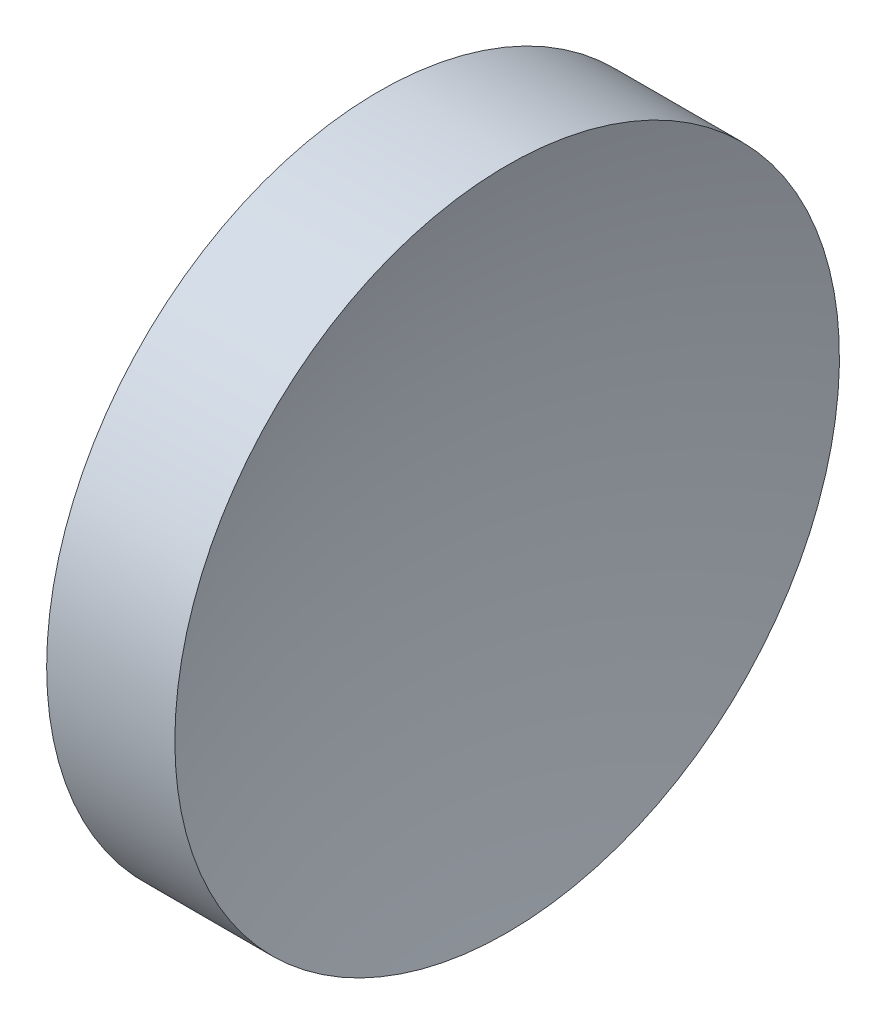
SolidWorks part; units mm, degrees
ref_plane "前视基准面" through (0, 0, 0) normal (0, 0, 1) x (1, 0, 0)
ref_plane "上视基准面" through (0, 0, 0) normal (0, 1, 0) x (1, 0, 0)
ref_plane "右视基准面" through (0, 0, 0) normal (1, 0, 0) x (0, 0, -1)
sketch "草图1" plane through (0, 0, 0) normal (0, 0, 1) x (1, 0, 0)
  line L0 (111.9552, 71.194) -> (137.836, 71.194) construction
  line L1 (119.5068, 71.194) -> (119.5068, 83.894)
  line L2 (119.5068, 83.894) -> (124.4066, 83.894)
  line L3 (122.5068, 71.194) -> (119.5068, 71.194)
  arc A0 (124.4066, 83.894) -> (122.5068, 71.194) centre (165.9068, 71.194) ccw
revolve "旋转1" add sketch "草图1" angle 360 about L0
